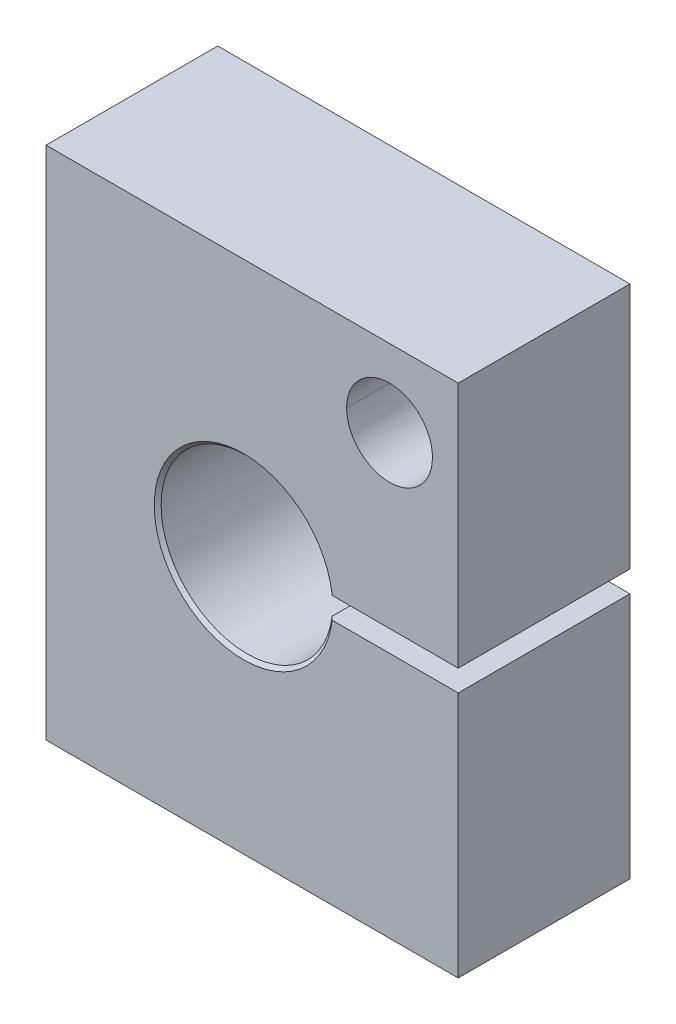
SolidWorks part; units mm, degrees
material "6061 Alloy"
ref_plane "Front" through (0, 0, 0) normal (0, 0, 1) x (1, 0, 0)
ref_plane "Top" through (0, 0, 0) normal (0, 1, 0) x (1, 0, 0)
ref_plane "Right" through (0, 0, 0) normal (1, 0, 0) x (0, 0, -1)
sketch "Sketch1" plane through (0, 0, 0) normal (0, 0, 1) x (1, 0, 0)
  line L1 (-15.24, 19.05) -> (15.24, 19.05)
  line L2 (-15.24, 19.05) -> (-15.24, -19.05)
  line L3 (-15.24, -19.05) -> (15.24, -19.05)
  line L4 (15.24, 19.05) -> (15.24, -19.05)
  line L5 (-15.24, 19.05) -> (15.24, -19.05) construction
  line L6 (-15.24, -19.05) -> (15.24, 19.05) construction
  point P0 (0, 0)
  dimension "D1" = 38.1
  dimension "D2" = 30.48
extrude "Boss-Extrude1" add sketch "Sketch1" along normal mid plane 12.7
sketch "Sketch2" plane through (0, 0, 6.35) normal (0, 0, 1) x (1, 0, 0)
  line L0 (15.24, 0.7937) -> (5.6652, 0.7937)
  line L1 (15.24, -19.05) -> (15.24, 19.05) construction
  line L2 (15.24, -0.7938) -> (5.6652, -0.7938)
  line L4 (-22.6132, 0) -> (31.9925, 0) construction
  line L5 (-0.635, 17.9885) -> (-0.635, -23.1021) construction
  line L7 (-15.24, 19.05) -> (-15.24, -19.05) construction
  line L9 (-15.24, -19.05) -> (15.24, -19.05) construction
  arc A0 (5.6652, 0.7937) -> (5.6652, -0.7938) centre (-0.635, 0) ccw
  dimension "D1" = 12.7
  dimension "D5" = 14.605
  dimension "D2" = 19.05
  dimension "D3" = 0.7937
  dimension "D4" = 0.7937
extrude "Cut-Extrude2" cut sketch "Sketch2" against normal through all flip side to cut
hole_wizard "1/4 (0.25) Diameter Hole1" positions "3DSketch4" profile "Sketch6" hole size "1/4" standard "ANSI Inch"
sketch3d "3DSketch4"
  line L0 (-15.24, -19.05, 6.35) -> (-15.24, -19.05, -6.35) construction
  line L2 (-15.24, -19.05, 0) -> (15.24, -19.05, 0) construction
  line L3 (15.24, -19.05, 6.35) -> (15.24, -19.05, -6.35) construction
  point P0 (8.89, -19.05, 0)
  dimension "D1" = 6.35
sketch "Sketch6" plane through (8.89, -19.05, 0) normal (1, 0, 0) x (0, 0, -1)
  line L0 (0, 0) -> (0, 9.5277)
  line L1 (0, 9.5277) -> (3.175, 7.62)
  line L2 (3.175, 7.62) -> (3.175, 0)
  line L5 (3.175, 0) -> (0, 0)
  line L10 (0, 9.5277) -> (-3.175, 7.62) construction
  line L11 (0, -6.35) -> (0, 107.95) construction
  dimension "Hole Dia." = 6.35
  dimension "Hole Depth" = 7.62
  dimension "Drill Angle" = 118
chamfer "Chamfer1" distance 0.254 angle 45 2 edges at (-6.985, 0, -6.35) (-6.985, 0, 6.35)
mirror "Mirror1" about plane through (0, 0, 0) normal (1, 0, 0) of "1/4 (0.25) Diameter Hole1"
sketch "Sketch8" plane through (0, 0, 6.35) normal (0, 0, 1) x (1, 0, 0)
  line L0 (15.24, 0.7937) -> (15.24, 19.05) construction
  line L1 (15.24, 19.05) -> (-15.24, 19.05) construction
  circle A0 centre (10.16, 13.335) radius 3.175
  dimension "D1" = 6.35
  dimension "D2" = 5.08
  dimension "D3" = 5.715
extrude "Cut-Extrude4" cut sketch "Sketch8" against normal through all
ref_plane "Plane1" through (0, 13.97, 0) normal (0, 1, 0) x (1, 0, 0)
ref_point "Point1"
split line "Split Line1"
